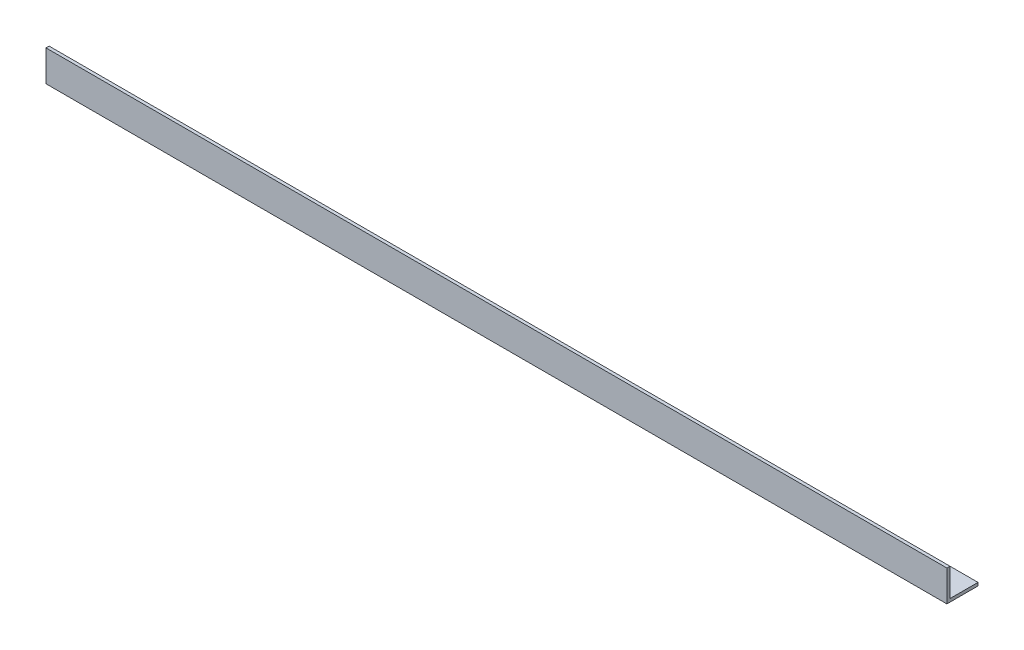
SolidWorks part; units mm, degrees
ref_plane "Спереди" through (0, 0, 0) normal (0, 0, 1) x (1, 0, 0)
ref_plane "Сверху" through (0, 0, 0) normal (0, 1, 0) x (1, 0, 0)
ref_plane "Справа" through (0, 0, 0) normal (1, 0, 0) x (0, 0, -1)
sketch "Эскиз1" plane through (0, 0, 0) normal (1, 0, 0) x (0, 0, -1)
  line L0 (0, 0) -> (0, 15)
  line L1 (0, 15) -> (1.5, 15)
  line L2 (1.5, 15) -> (1.5, 1.5)
  line L3 (1.5, 1.5) -> (15, 1.5)
  line L4 (15, 1.5) -> (15, 0)
  line L5 (15, 0) -> (0, 0)
  dimension "D1" = 15
  dimension "D2" = 15
  dimension "D3" = 1.5
  dimension "D4" = 1.5
extrude "Бобышка-Вытянуть1" add sketch "Эскиз1" along normal blind 434.5
